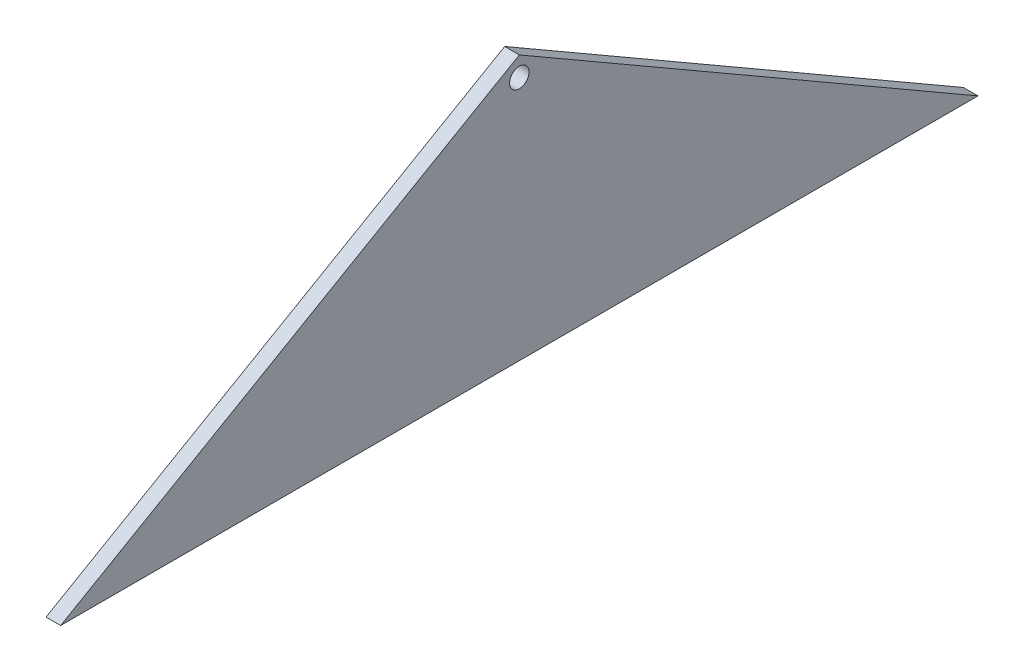
SolidWorks part; units mm, degrees
ref_plane "Front Plane" through (0, 0, 0) normal (0, 0, 1) x (1, 0, 0)
ref_plane "Top Plane" through (0, 0, 0) normal (0, 1, 0) x (1, 0, 0)
ref_plane "Right Plane" through (0, 0, 0) normal (1, 0, 0) x (0, 0, -1)
sketch "Sketch1" plane through (0, 0, 0) normal (1, 0, 0) x (0, 0, -1)
  line L0 (-94, 0) -> (94, 0)
  line L1 (-94, 0) -> (0, 54.2709)
  line L2 (0, 54.2709) -> (94, 0)
  line L3 (-94, 0) -> (-100, 0) construction
  line L4 (-100, 0) -> (0, 57.735) construction
  line L5 (0, 57.735) -> (100, 0) construction
  line L6 (100, 0) -> (94, 0) construction
  circle A0 centre (0, 50.2709) radius 2
  point P4 (0, 0)
  point P10 (0, 0)
  dimension "D4" = 4
  dimension "D1" = 3
  dimension "D2" = 30
  dimension "D3" = 200
  dimension "D5" = 4
extrude "Boss-Extrude1" add sketch "Sketch1" along normal blind 3
